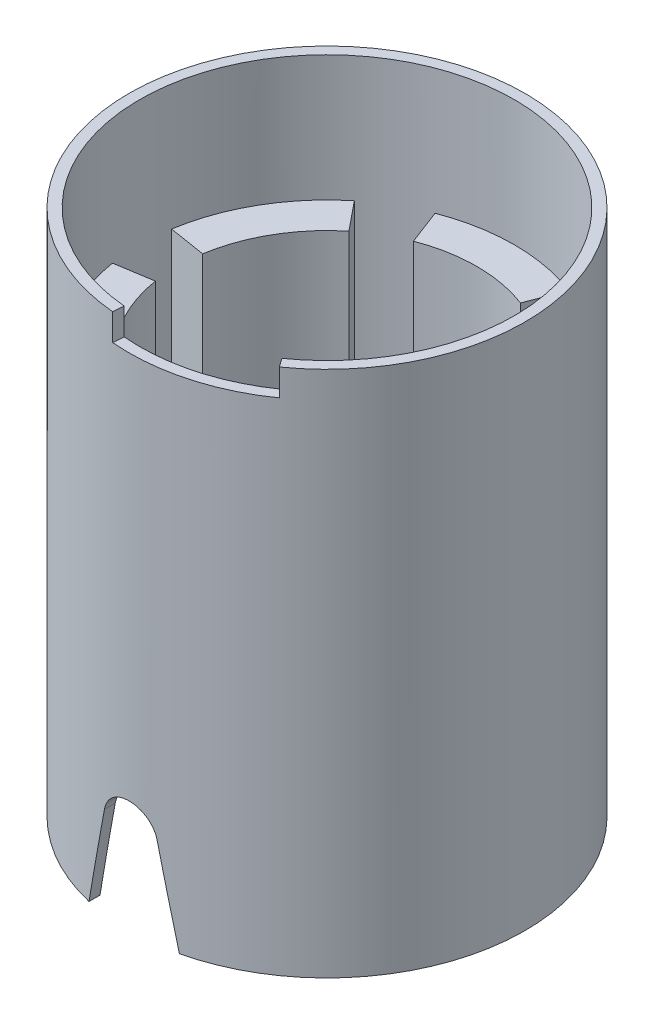
SolidWorks part; units mm, degrees
ref_plane "Front Plane" through (0, 0, 0) normal (0, 0, 1) x (1, 0, 0)
ref_plane "Top Plane" through (0, 0, 0) normal (0, 1, 0) x (1, 0, 0)
ref_plane "Right Plane" through (0, 0, 0) normal (1, 0, 0) x (0, 0, -1)
sketch "Sketch1" plane through (0, 0, 0) normal (0, 1, 0) x (1, 0, 0)
  line L0 (0, 37) -> (0, -37) construction
  line L2 (-37, 0) -> (37, 0) construction
  circle A0 centre (0, 0) radius 37
  circle A1 centre (0, 0) radius 35
  dimension "D1" = 74
  dimension "D2" = 2
extrude "Boss-Extrude1" add sketch "Sketch1" along normal blind 98.5
ref_plane "Plane1" through (0, 0, 37) normal (0, 0, 1) x (1, 0, 0)
sketch "Sketch2" plane through (0, 0, 37) normal (0, 0, 1) x (1, 0, 0)
  line L0 (0, 0) -> (0, 1.2469) construction
  line L1 (0, 21) -> (0, 0) construction
  line L2 (-8.45, 0) -> (-4.9168, 17)
  line L3 (35, 0) -> (-35, 0) construction
  line L4 (-8.45, 0) -> (8.45, 0)
  line L5 (8.45, 0) -> (4.9168, 17)
  arc A0 (-4.9168, 17) -> (4.9168, 17) centre (0, 15.9781) cw
  dimension "D1" = 21
  dimension "D3" = 8.45
  dimension "D4" = 17
extrude "Cut-Extrude2" cut sketch "Sketch2" against normal up to surface (2.3471 mm away)
sketch "Sketch4" plane through (0, 98.5, 0) normal (0, 1, 0) x (1, 0, 0)
  line L0 (20.173, -28.6016) -> (21.3257, -30.236)
  line L2 (0, 0) -> (0, -45.6555) construction
  line L3 (-3.2, -36.8614) -> (-3.027, -34.8689)
  arc A0 (-3.2, -36.8614) -> (21.3257, -30.236) centre (0, 0) ccw
  circle A1 centre (0, 0) radius 37 construction
  circle A2 centre (0, 0) radius 35 construction
  arc A3 (-3.027, -34.8689) -> (20.173, -28.6016) centre (0, 0) ccw
  dimension "D1" = 3.2
  dimension "D3" = 23.2
extrude "Cut-Extrude3" cut sketch "Sketch4" against normal blind 5
ref_plane "Plane2" through (0, 33, 0) normal (0, 1, 0) x (1, 0, 0)
sketch "Sketch5" plane through (0, 33, 0) normal (0, 1, 0) x (1, 0, 0)
  line L0 (0, 32.314) -> (0, -42.5028) construction
  line L1 (-12.5, -32.6917) -> (-10, -26.1534)
  line L2 (12.5, -32.6917) -> (10, -26.1534)
  arc A0 (-12.5, -32.6917) -> (12.5, -32.6917) centre (0, 0) ccw
  arc A1 (20.173, -28.6016) -> (-3.027, -34.8689) centre (0, 0) ccw construction
  arc A2 (-3.027, -34.8689) -> (20.173, -28.6016) centre (0, 0) ccw construction
  arc A3 (-10, -26.1534) -> (10, -26.1534) centre (0, 0) ccw
  dimension "D1" = 7
  dimension "D2" = 25
  dimension "D3" = 12.5
extrude "Boss-Extrude2" add sketch "Sketch5" along normal blind 42
pattern_circular "CirPattern1" count 6 over 360 about axis through (0, 0, 0) along (0, 1, 0) of "Boss-Extrude2"
